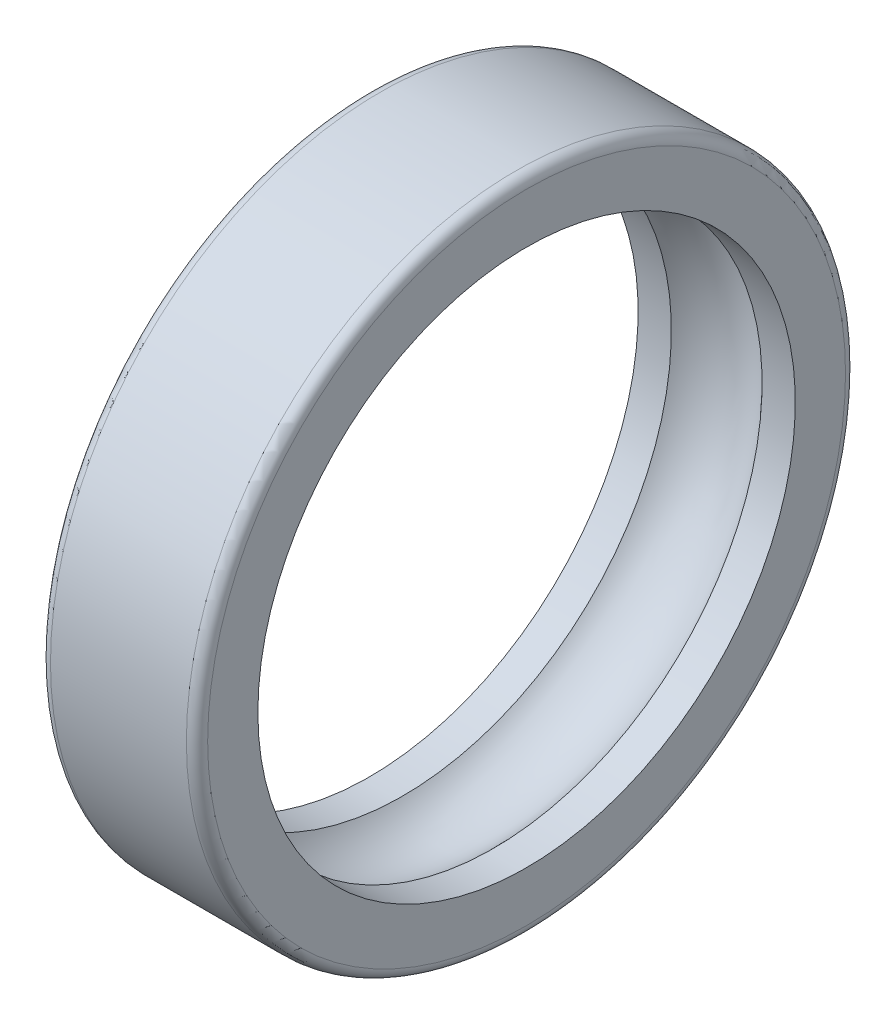
SolidWorks part; units mm, degrees
ref_plane "Płaszczyzna przednia" through (0, 0, 0) normal (0, 0, 1) x (1, 0, 0)
ref_plane "Płaszczyzna górna" through (0, 0, 0) normal (0, 1, 0) x (1, 0, 0)
ref_plane "Płaszczyzna prawa" through (0, 0, 0) normal (1, 0, 0) x (0, 0, -1)
sketch "Sketch1" plane through (0, 0, 0) normal (0, 0, 1) x (1, 0, 0)
  line L0 (0, 0) -> (34.0699, 0) construction
  line L1 (0, 53) -> (0, 0) construction
  line L2 (-15.5, 65) -> (15.5, 65)
  line L3 (-15.5, 65) -> (-15.5, 53)
  line L4 (-15.5, 53) -> (-8.9443, 53)
  line L5 (15.5, 65) -> (15.5, 53)
  line L6 (-15.5, 65) -> (15.5, 53) construction
  line L7 (-15.5, 53) -> (15.5, 65) construction
  line L8 (8.9443, 53) -> (15.5, 53)
  arc A0 (-8.9443, 53) -> (8.9443, 53) centre (0, 45) cw
  point P3 (0, 59)
  dimension "D5" = 12
  dimension "D1" = 31
  dimension "D2" = 53
  dimension "D3" = 65
  dimension "D4" = 8
revolve "Revolve1" add sketch "Sketch1" angle 360 about L0
fillet "Fillet1" radius 2.1 2 edges at (-15.5, 0, 65) (15.5, 0, 65)
